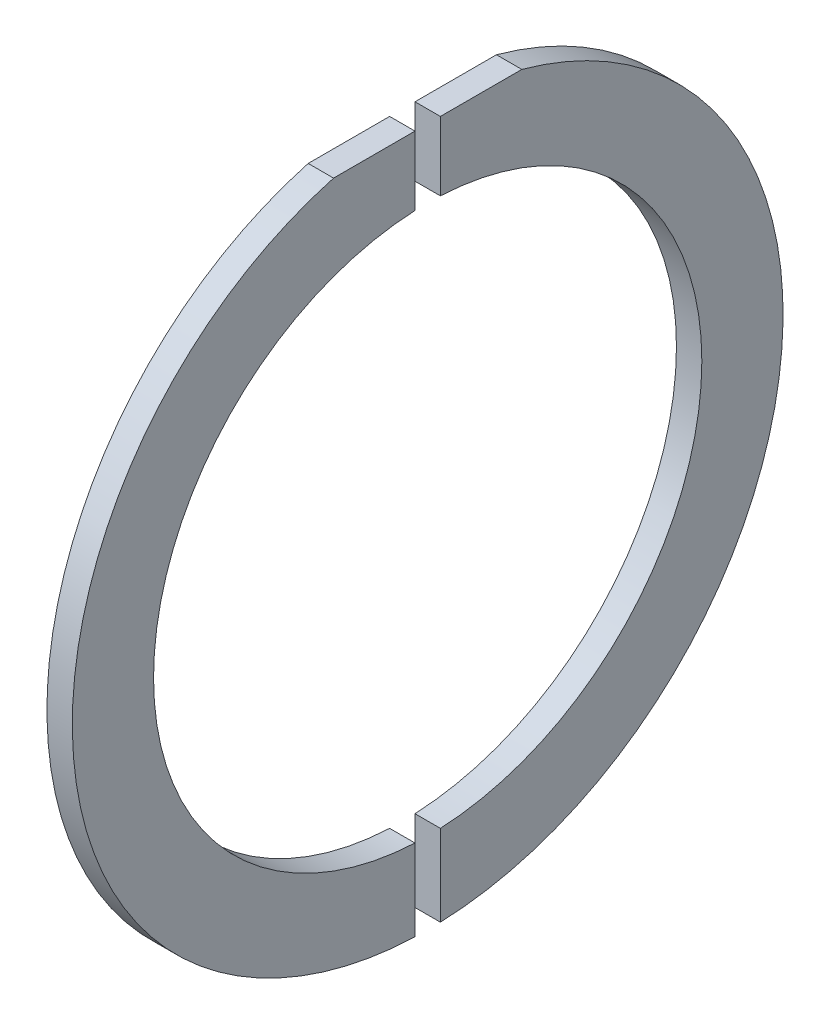
SolidWorks part; units mm, degrees
material "2024-T4"
ref_plane "Спереди" through (0, 0, 0) normal (0, 0, 1) x (1, 0, 0)
ref_plane "Сверху" through (0, 0, 0) normal (0, 1, 0) x (1, 0, 0)
ref_plane "Справа" through (0, 0, 0) normal (1, 0, 0) x (0, 0, -1)
sketch "Эскиз1" plane through (0, 0, 0) normal (0, 1, 0) x (1, 0, 0)
  line L0 (0, 21.6) -> (-2, 21.6)
  line L1 (-2, 21.6) -> (-2, 28)
  line L2 (-2, 28) -> (0, 28)
  line L3 (0, 28) -> (0, 21.6)
  line L6 (-20.8659, 0) -> (16.831, 0) construction
  dimension "D2" = 21.6
  dimension "D4" = 28
  dimension "D5" = 2
revolve "Повернуть1" add sketch "Эскиз1" angle 360 about L6
sketch "Эскиз2" plane through (0, 0, 0) normal (1, 0, 0) x (0, 0, -1)
  line L0 (1, -27.9821) -> (1, 27)
  line L1 (-1, -27.9821) -> (-1, 27)
  line L2 (-1, 27) -> (-7.4162, 27)
  line L3 (1, 27) -> (7.4162, 27)
  circle A0 centre (0, 0) radius 28 construction
  circle M6 centre (0, 0) radius 28
  circle M8 centre (0, 0) radius 21.6
  dimension "D2" = 27
  dimension "D1" = 2
  dimension "D3" = 1
extrude "Вырез-Вытянуть1" cut sketch "Эскиз2" against normal through all contours L1 L0 M8 M6 | L1 L0 M6 M8
